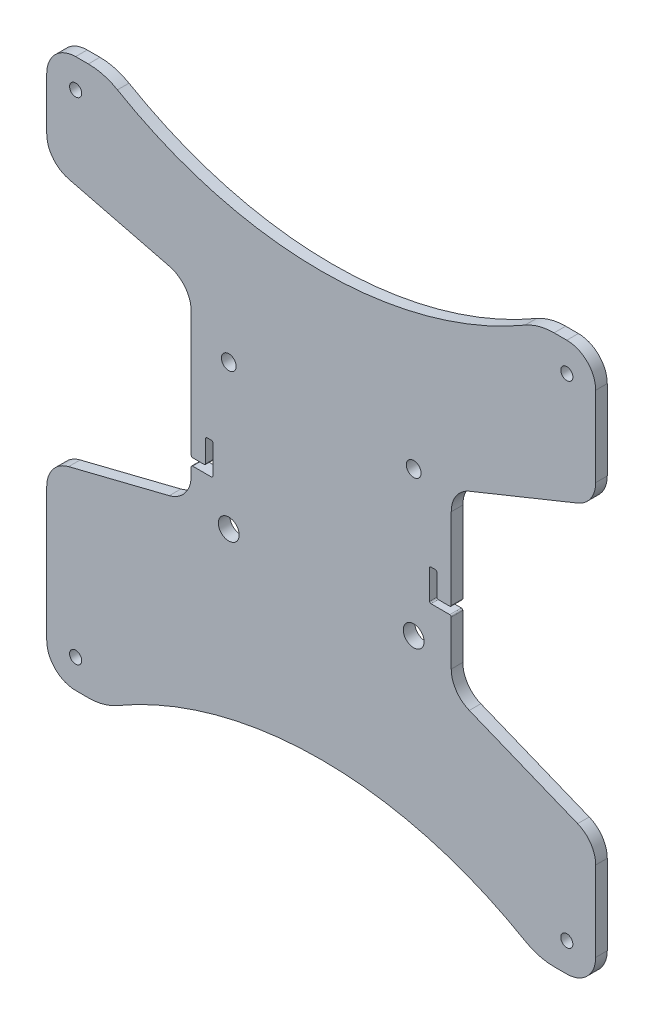
SolidWorks part; units mm, degrees
ref_plane "Front Plane" through (0, 0, 0) normal (0, 0, 1) x (1, 0, 0)
ref_plane "Top Plane" through (0, 0, 0) normal (0, 1, 0) x (1, 0, 0)
ref_plane "Right Plane" through (0, 0, 0) normal (1, 0, 0) x (0, 0, -1)
ref_plane "Plane1" through (0, 0, 0) normal (0, 0, -1) x (-1, 0, 0)
sketch "Sketch1" plane through (0, 0, 0) normal (0, 0, -1) x (-1, 0, 0)
  line L0 (87.4254, -29.1063) -> (52.5746, -20.3937)
  line L1 (45, -10.6922) -> (45, -8)
  line L2 (44.5, -7.5) -> (38, -7.5)
  line L3 (37.5, -7) -> (37.5, 3)
  line L4 (38, 3.5) -> (39.5, 3.5)
  line L5 (40, 3) -> (40, -4.5)
  line L6 (40.5, -5) -> (44.5, -5)
  line L7 (45, -4.5) -> (45, 38.6922)
  line L8 (52.5746, 48.3937) -> (87.4254, 57.1063)
  line L9 (95, 66.8078) -> (95, 85)
  line L10 (85, 95) -> (80.6, 95)
  line L11 (-80.6, 95) -> (-85, 95)
  line L12 (-95, 85) -> (-95, 57.3099)
  line L13 (-88.7544, 48.0415) -> (-51.2456, 32.8477)
  line L14 (-45, 23.5792) -> (-45, -4.5)
  line L15 (-44.5, -5) -> (-40.5, -5)
  line L16 (-40, -4.5) -> (-40, 3)
  line L17 (-39.5, 3.5) -> (-38, 3.5)
  line L18 (-37.5, 3) -> (-37.5, -7)
  line L19 (-38, -7.5) -> (-44.5, -7.5)
  line L20 (-45, -8) -> (-45, -23.5792)
  line L21 (-51.2456, -32.8477) -> (-88.7544, -48.0415)
  line L22 (-95, -57.3099) -> (-95, -85)
  line L23 (-85, -95) -> (-80.6, -95)
  line L24 (80.6, -95) -> (85, -95)
  line L25 (95, -85) -> (95, -38.8078)
  circle A0 centre (-85, -85) radius 2.1
  circle A1 centre (-85, 85) radius 2.1
  circle A2 centre (85, 85) radius 2.1
  circle A3 centre (85, -85) radius 2.1
  circle A4 centre (32, 29.9) radius 2.55
  circle A5 centre (32, -20.1) radius 3.6
  circle A6 centre (-32, -20.1) radius 3.6
  circle A7 centre (-32, 29.9) radius 2.55
  arc A8 (52.5746, -20.3937) -> (45, -10.6922) centre (55, -10.6922) cw
  arc A9 (45, -8) -> (44.5, -7.5) centre (44.5, -8) ccw
  arc A10 (38, -7.5) -> (37.5, -7) centre (38, -7) cw
  arc A11 (37.5, 3) -> (38, 3.5) centre (38, 3) cw
  arc A12 (39.5, 3.5) -> (40, 3) centre (39.5, 3) cw
  arc A13 (40, -4.5) -> (40.5, -5) centre (40.5, -4.5) ccw
  arc A14 (44.5, -5) -> (45, -4.5) centre (44.5, -4.5) ccw
  arc A15 (45, 38.6922) -> (52.5746, 48.3937) centre (55, 38.6922) cw
  arc A16 (87.4254, 57.1063) -> (95, 66.8078) centre (85, 66.8078) ccw
  arc A17 (95, 85) -> (85, 95) centre (85, 85) ccw
  arc A18 (80.6, 95) -> (70.525, 92.277) centre (80.6, 75) ccw
  arc A19 (70.525, 92.277) -> (-70.525, 92.277) centre (0, 213.2159) cw
  arc A20 (-70.525, 92.277) -> (-80.6, 95) centre (-80.6, 75) ccw
  arc A21 (-85, 95) -> (-95, 85) centre (-85, 85) ccw
  arc A22 (-95, 57.3099) -> (-88.7544, 48.0415) centre (-85, 57.3099) ccw
  arc A23 (-51.2456, 32.8477) -> (-45, 23.5792) centre (-55, 23.5792) cw
  arc A24 (-45, -4.5) -> (-44.5, -5) centre (-44.5, -4.5) ccw
  arc A25 (-40.5, -5) -> (-40, -4.5) centre (-40.5, -4.5) ccw
  arc A26 (-40, 3) -> (-39.5, 3.5) centre (-39.5, 3) cw
  arc A27 (-38, 3.5) -> (-37.5, 3) centre (-38, 3) cw
  arc A28 (-37.5, -7) -> (-38, -7.5) centre (-38, -7) cw
  arc A29 (-44.5, -7.5) -> (-45, -8) centre (-44.5, -8) ccw
  arc A30 (-45, -23.5792) -> (-51.2456, -32.8477) centre (-55, -23.5792) cw
  arc A31 (-88.7544, -48.0415) -> (-95, -57.3099) centre (-85, -57.3099) ccw
  arc A32 (-95, -85) -> (-85, -95) centre (-85, -85) ccw
  arc A33 (-80.6, -95) -> (-70.525, -92.277) centre (-80.6, -75) ccw
  arc A34 (-70.525, -92.277) -> (70.525, -92.277) centre (0, -213.2159) cw
  arc A35 (70.525, -92.277) -> (80.6, -95) centre (80.6, -75) ccw
  arc A36 (85, -95) -> (95, -85) centre (85, -85) ccw
  arc A37 (95, -38.8078) -> (87.4254, -29.1063) centre (85, -38.8078) ccw
  point P98 (0, 0)
  point P99 (0, 0)
  point P100 (0, 0)
  dimension "D1" = 13
  dimension "D2" = 13
  dimension "D3" = 74.9
  dimension "D4" = 50
extrude "Boss-Extrude1" add sketch "Sketch1" against normal blind 4
